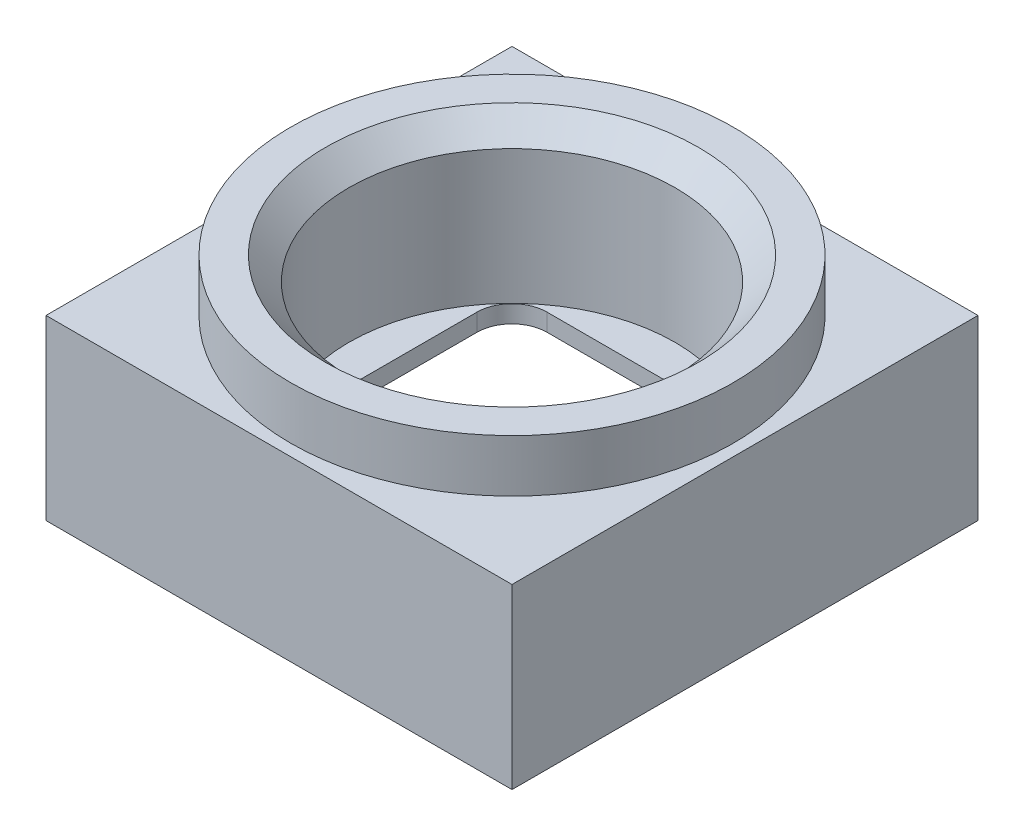
SolidWorks part; units mm, degrees
material "ABS PC"
ref_plane "Vorne" through (0, 0, 0) normal (0, 0, 1) x (1, 0, 0)
ref_plane "Oben" through (0, 0, 0) normal (0, 1, 0) x (1, 0, 0)
ref_plane "Rechts" through (0, 0, 0) normal (1, 0, 0) x (0, 0, -1)
sketch "downside" plane through (0, 0, 0) normal (0, 1, 0) x (1, 0, 0)
  line L0 (-4, 4) -> (4, -4) construction
  line L1 (-4, 4) -> (4, 4) construction
  line L2 (-4, 4) -> (-4, -4) construction
  line L3 (-4, -4) -> (4, -4) construction
  line L4 (4, 4) -> (4, -4) construction
  dimension "D1" = 8
sketch "Skizze2" plane through (0, 0, 0) normal (0, 1, 0) x (1, 0, 0)
  line L0 (-4, 4) -> (4, 4) construction
  line L1 (-4, 4) -> (-4, -4) construction
  line L2 (4, 4) -> (4, -4) construction
  line L3 (-4, -4) -> (4, -4) construction
  line L4 (-4, 4) -> (4, 4)
  line L5 (-4, 4) -> (-4, -4)
  line L6 (4, 4) -> (4, -4)
  line L7 (-4, -4) -> (4, -4)
  line L8 (-3.7, 3.7) -> (3.7, 3.7)
  line L9 (3.7, 3.7) -> (3.7, -3.7)
  line L10 (-3.7, -3.7) -> (3.7, -3.7)
  line L11 (-3.7, 3.7) -> (-3.7, -3.7)
  dimension "D1" = 0.3
extrude "Aufsatz-Linear austragen1" add sketch "Skizze2" along normal blind 0.6
sketch "Skizze5" plane through (0, 0.6, 0) normal (0, 1, 0) x (1, 0, 0)
  line L0 (0, 0) -> (0, 3.2) construction
  line L1 (-2.7646, 3.2) -> (2.7646, 3.2)
  line L2 (-2.7646, -3.2) -> (2.7646, -3.2)
  line L3 (-3.2, 2.7646) -> (-3.2, -2.7646)
  line L4 (3.2, 2.7646) -> (3.2, -2.7646)
  line L5 (0, 0) -> (3.2, 0) construction
  line L11 (-4, 4) -> (-4, -4)
  line L12 (-4, -4) -> (4, -4)
  line L13 (4, -4) -> (4, 4)
  line L14 (4, 4) -> (-4, 4)
  line L15 (-4, 4) -> (-4, -4)
  line L16 (-4, -4) -> (4, -4)
  line L17 (4, -4) -> (4, 4)
  line L18 (4, 4) -> (-4, 4)
  arc A0 (3.2, 2.7646) -> (2.7646, 3.2) centre (3.1, 3.1) ccw
  arc A1 (3.2, -2.7646) -> (2.7646, -3.2) centre (3.1, -3.1) cw
  arc A2 (-3.2, -2.7646) -> (-2.7646, -3.2) centre (-3.1, -3.1) ccw
  arc A3 (-3.2, 2.7646) -> (-2.7646, 3.2) centre (-3.1, 3.1) cw
  point P17 (0, -3.2)
  dimension "D1" = 0.7
  dimension "D2" = 6.4
  dimension "D3" = 0.1
  dimension "D4" = 0
extrude "Aufsatz-Linear austragen3" add sketch "Skizze5" along normal blind 0.35
sketch "Skizze4" plane through (0, 0.95, 0) normal (0, 1, 0) x (1, 0, 0)
  line L0 (0, 2.15) -> (0, -2.15) construction
  line L1 (-1.55, 2.15) -> (1.55, 2.15)
  line L2 (-2.15, 1.55) -> (-2.15, -1.55)
  line L3 (-1.55, -2.15) -> (1.55, -2.15)
  line L4 (2.15, 1.55) -> (2.15, -1.55)
  line L9 (4, 4) -> (-4, 4)
  line L10 (-4, 4) -> (-4, -4)
  line L11 (-4, -4) -> (4, -4)
  line L12 (4, -4) -> (4, 4)
  line L13 (4, 4) -> (-4, 4)
  line L14 (-4, 4) -> (-4, -4)
  line L15 (-4, -4) -> (4, -4)
  line L16 (4, -4) -> (4, 4)
  arc A0 (-2.15, -1.55) -> (-1.55, -2.15) centre (-1.55, -1.55) ccw
  arc A1 (1.55, -2.15) -> (2.15, -1.55) centre (1.55, -1.55) ccw
  arc A2 (1.55, 2.15) -> (2.15, 1.55) centre (1.55, 1.55) cw
  arc A3 (-1.55, 2.15) -> (-2.15, 1.55) centre (-1.55, 1.55) ccw
  dimension "D1" = 0.6
  dimension "D2" = 4.3
  dimension "D3" = 0
extrude "Aufsatz-Linear austragen2" add sketch "Skizze4" along normal blind 0.3
sketch "Skizze7" plane through (0, 1.25, 0) normal (0, 1, 0) x (1, 0, 0)
  line L4 (4, -4) -> (4, 4)
  line L5 (4, 4) -> (-4, 4)
  line L6 (-4, 4) -> (-4, -4)
  line L7 (-4, -4) -> (4, -4)
  line L8 (4, -4) -> (4, 4)
  line L9 (4, 4) -> (-4, 4)
  line L10 (-4, 4) -> (-4, -4)
  line L11 (-4, -4) -> (4, -4)
  circle A0 centre (0, 0) radius 2.8
  dimension "D2" = 5.6
  dimension "D1" = 0
extrude "Aufsatz-Linear austragen4" add sketch "Skizze7" along normal blind 1.8
cosmetic thread "Gewindedarstellung1" parameters "D1"=2.1, "D2"=6
sketch "Skizze8" plane through (0, 3.05, 0) normal (0, 1, 0) x (1, 0, 0)
  circle A0 centre (0, 0) radius 3.8
  circle A1 centre (0, 0) radius 2.8 construction
  circle A2 centre (0, 0) radius 2.8
  dimension "D1" = 7.6
extrude "Aufsatz-Linear austragen5" add sketch "Skizze8" along normal blind 0.9
chamfer "Fase1" distance 0.4 angle 45 1 edges at (0, 3.95, 2.8)
